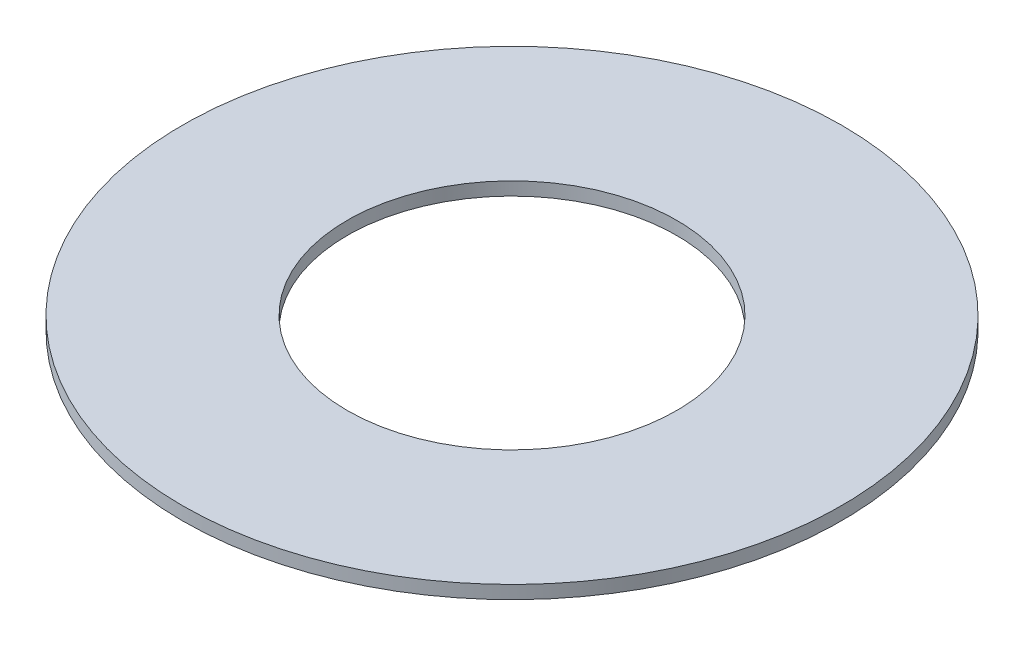
SolidWorks part; units mm, degrees
material "AISI 304"
ref_plane "Front Plane" through (0, 0, 0) normal (0, 0, 1) x (1, 0, 0)
ref_plane "Top Plane" through (0, 0, 0) normal (0, 1, 0) x (1, 0, 0)
ref_plane "Right Plane" through (0, 0, 0) normal (1, 0, 0) x (0, 0, -1)
sketch "Sketch1" plane through (0, 0, 0) normal (0, 1, 0) x (1, 0, 0)
  circle A0 centre (0, 0) radius 5
  circle A1 centre (0, 0) radius 2.5
  dimension "D1" = 5
  dimension "D2" = 10
extrude "Boss-Extrude1" add sketch "Sketch1" along normal blind 0.2
